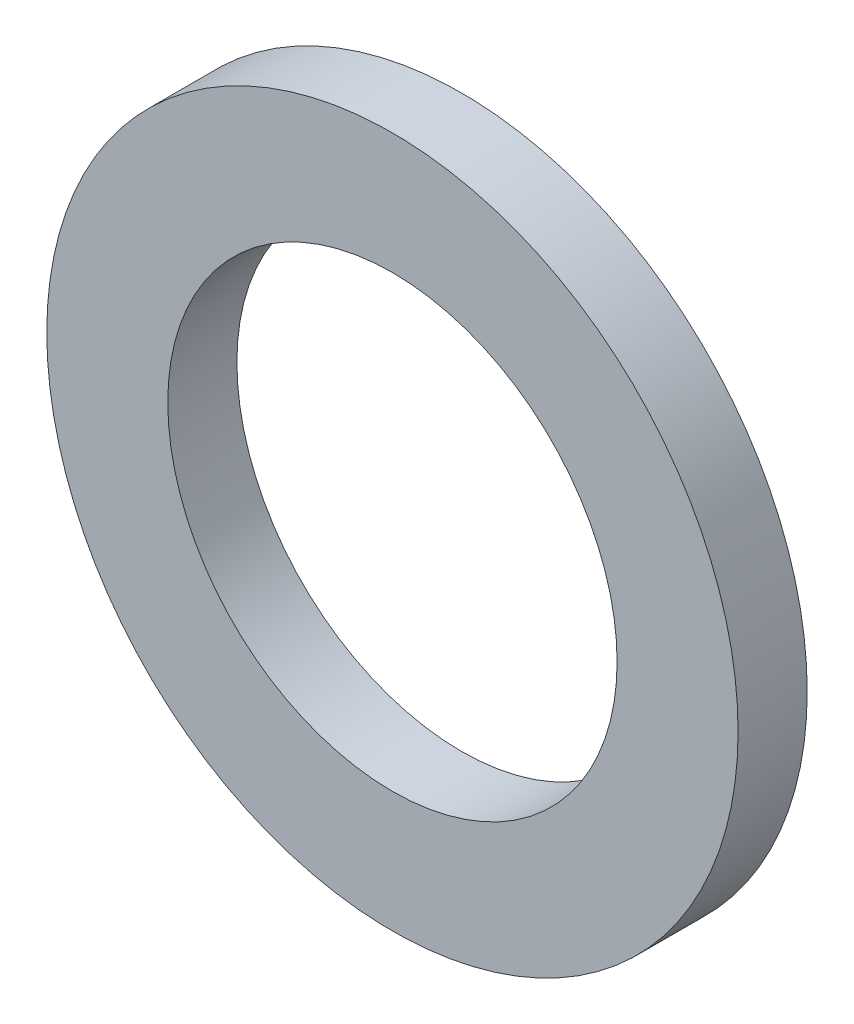
SolidWorks part; units mm, degrees
ref_plane "Alzado" through (0, 0, 0) normal (0, 0, 1) x (1, 0, 0)
ref_plane "Planta" through (0, 0, 0) normal (0, 1, 0) x (1, 0, 0)
ref_plane "Vista lateral" through (0, 0, 0) normal (1, 0, 0) x (0, 0, -1)
sketch "Croquis1" plane through (0, 0, 0) normal (0, 0, 1) x (1, 0, 0)
  circle A0 centre (0, 0) radius 3.25
  circle A1 centre (0, 0) radius 5
  dimension "D1" = 6.5
  dimension "D2" = 10
extrude "Saliente-Extruir1" add sketch "Croquis1" along normal blind 1
